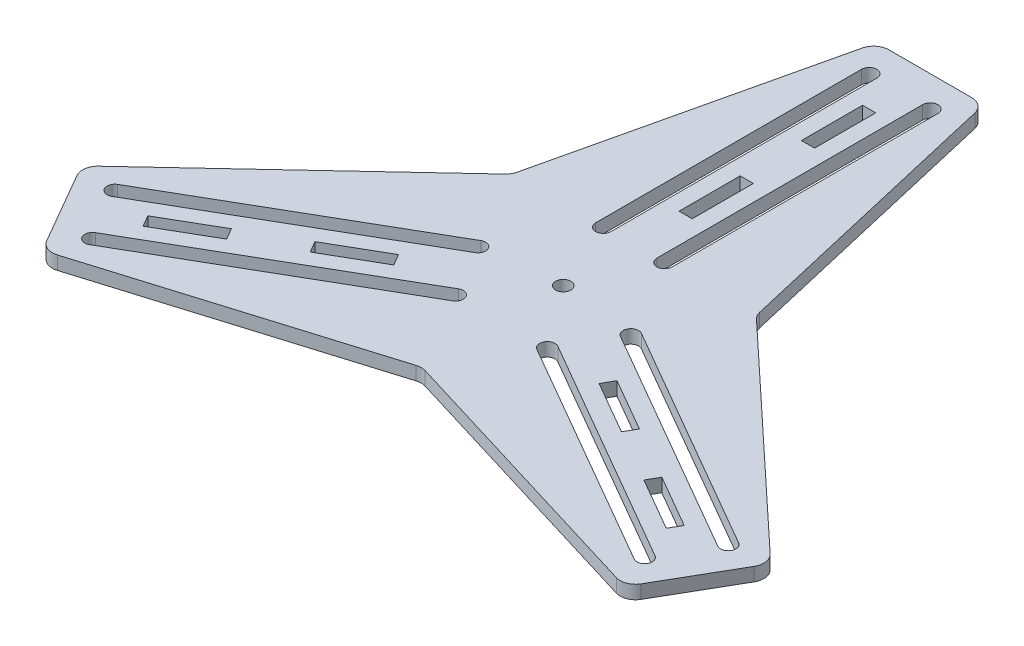
SolidWorks part; units mm, degrees
material "Acrylic (Medium-high impact)"
ref_plane "Front Plane" through (0, 0, 0) normal (0, 0, 1) x (1, 0, 0)
ref_plane "Top Plane" through (0, 0, 0) normal (0, 1, 0) x (1, 0, 0)
ref_plane "Right Plane" through (0, 0, 0) normal (1, 0, 0) x (0, 0, -1)
sketch "Sketch1" plane through (0, 0, 0) normal (0, 1, 0) x (1, 0, 0)
  line L0 (0, 0) -> (50.8, 29.3294)
  line L1 (50.8, 29.3294) -> (22.225, 152.4)
  line L2 (22.225, 152.4) -> (-22.225, 152.4)
  line L3 (-22.225, 152.4) -> (-50.8, 29.3294)
  line L4 (-50.8, 29.3294) -> (0, 0)
  line L5 (-12.7, 29.3294) -> (-12.7, 139.7) construction
  line L6 (0, 0) -> (0, 152.4) construction
  line L7 (-9.525, 29.3294) -> (-9.525, 139.7)
  line L8 (-15.875, 29.3294) -> (-15.875, 139.7)
  line L9 (2.7305, 63.5) -> (0, 63.5) construction
  line L10 (-2.7305, 50.8) -> (2.7305, 50.8)
  line L11 (-2.7305, 50.8) -> (-2.7305, 76.2)
  line L12 (12.7, 29.3294) -> (12.7, 139.7) construction
  line L13 (9.525, 29.3294) -> (9.525, 139.7)
  line L14 (15.875, 29.3294) -> (15.875, 139.7)
  line L15 (-2.7305, 76.2) -> (2.7305, 76.2)
  line L16 (2.7305, 50.8) -> (2.7305, 76.2)
  line L17 (0, 63.5) -> (-2.7305, 63.5) construction
  line L18 (2.7305, 114.3) -> (0, 114.3) construction
  line L19 (-2.7305, 101.6) -> (2.7305, 101.6)
  line L20 (-2.7305, 101.6) -> (-2.7305, 127)
  line L21 (-2.7305, 127) -> (2.7305, 127)
  line L22 (2.7305, 101.6) -> (2.7305, 127)
  line L23 (0, 114.3) -> (-2.7305, 114.3) construction
  arc A0 (9.525, 29.3294) -> (15.875, 29.3294) centre (12.7, 29.3294) ccw
  arc A1 (15.875, 139.7) -> (9.525, 139.7) centre (12.7, 139.7) ccw
  arc A2 (-9.525, 29.3294) -> (-15.875, 29.3294) centre (-12.7, 29.3294) cw
  arc A3 (-15.875, 139.7) -> (-9.525, 139.7) centre (-12.7, 139.7) cw
  point P9 (12.7, 84.5147)
  point P12 (-12.7, 84.5147)
  point P18 (0, 0)
  dimension "D1" = 120
  dimension "D2" = 44.45
  dimension "D3" = 50.8
  dimension "D4" = 152.4
  dimension "D6" = 6.35
  dimension "D7" = 12.7
  dimension "D5" = 12.7
  dimension "D8" = 25.4
  dimension "D9" = 5.461
  dimension "D10" = 2
  dimension "D11" = 50.8
  dimension "D12" = 101.6
extrude "Boss-Extrude1" add sketch "Sketch1" along normal blind 5.588
pattern_circular "CirPattern1" count 3 over 360 about axis through (0, 0, 0) along (0, 1, 0) of "Boss-Extrude1"
sketch "Sketch3" plane through (0, 5.588, 0) normal (0, 1, 0) x (1, 0, 0)
  circle A0 centre (0, 0) radius 3.175
  dimension "D1" = 6.35
extrude "Cut-Extrude1" cut sketch "Sketch3" against normal through all
fillet "Fillet2" radius 6.35 9 edges at (50.8, 2.794, -29.3294) (143.0948, 2.794, 56.9526) (120.8698, 2.794, 95.4474) (0, 2.794, 58.6588) (-120.8698, 2.794, 95.4474) (-143.0948, 2.794, 56.9526) (-50.8, 2.794, -29.3294) (-22.225, 2.794, -152.4) (22.225, 2.794, -152.4)
